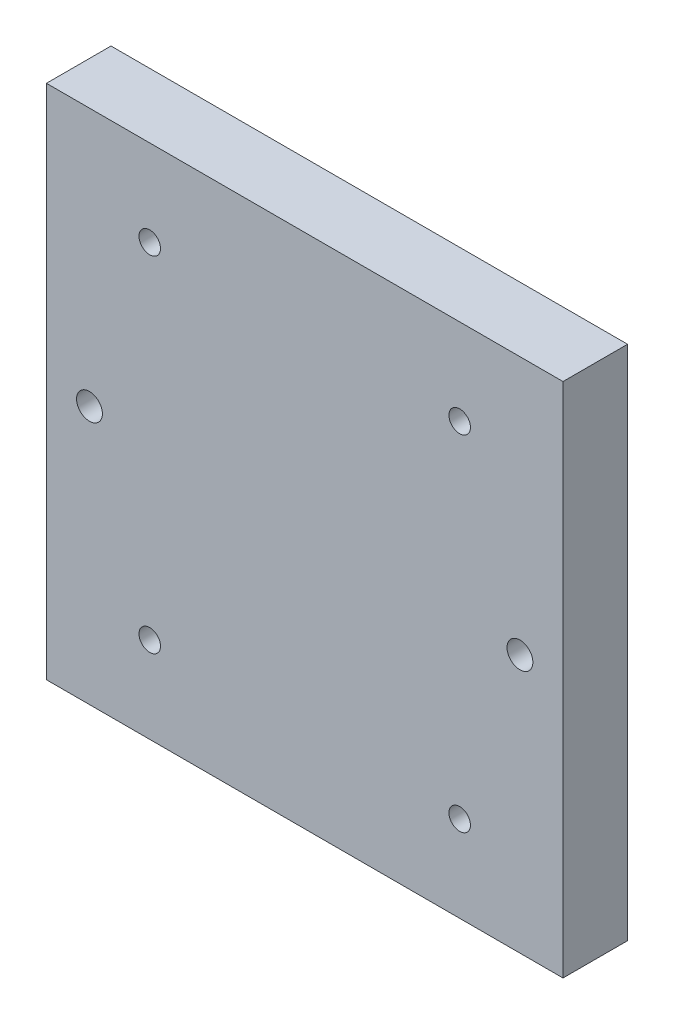
SolidWorks part; units mm, degrees
ref_plane "Front Plane" through (0, 0, 0) normal (0, 0, 1) x (1, 0, 0)
ref_plane "Top Plane" through (0, 0, 0) normal (0, 1, 0) x (1, 0, 0)
ref_plane "Right Plane" through (0, 0, 0) normal (1, 0, 0) x (0, 0, -1)
sketch "Sketch1" plane through (0, 0, 0) normal (0, 0, 1) x (1, 0, 0)
  line L1 (-60, 60) -> (60, 60)
  line L2 (-60, 60) -> (-60, -60)
  line L3 (-60, -60) -> (60, -60)
  line L4 (60, 60) -> (60, -60)
  line L5 (-60, 60) -> (60, -60) construction
  line L6 (-60, -60) -> (60, 60) construction
  point P0 (0, 0)
  dimension "D1" = 120
  dimension "D2" = 120
extrude "Boss-Extrude1" add sketch "Sketch1" against normal blind 15
sketch "Sketch7" plane through (0, 0, -15) normal (0, 0, -1) x (-1, 0, 0)
  line L0 (0, 0) -> (0, 40) construction
  line L1 (0, 0) -> (50, 0) construction
  line L3 (0, 0) -> (-36, 0) construction
  line L4 (-36, 0) -> (-36, -40) construction
  circle A4 centre (-36, -40) radius 2.5
  circle A5 centre (-36, 40) radius 2.5
  circle A6 centre (36, -40) radius 2.5
  circle A7 centre (36, 40) radius 2.5
  circle A8 centre (50, 0) radius 3
  circle A9 centre (-50, 0) radius 3
extrude "Cut-Extrude4" cut sketch "Sketch7" against normal up to next
